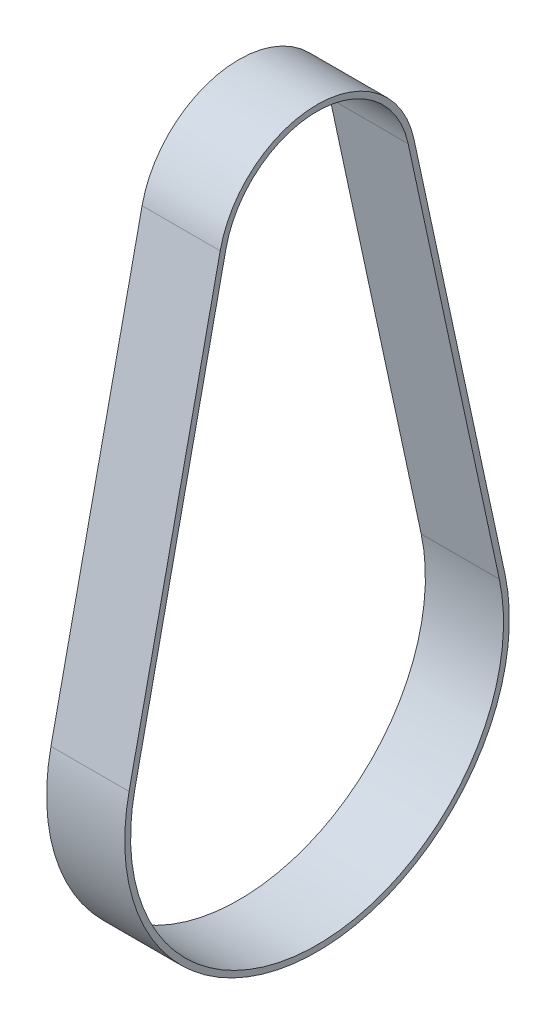
SolidWorks part; units mm, degrees
material "POLYURETHANE (11671)"
ref_plane "Front Plane" through (0, 0, 0) normal (0, 0, 1) x (1, 0, 0)
ref_plane "Top Plane" through (0, 0, 0) normal (0, 1, 0) x (1, 0, 0)
ref_plane "Right Plane" through (0, 0, 0) normal (1, 0, 0) x (0, 0, -1)
sketch "Sketch1" plane through (0, 0, 0) normal (1, 0, 0) x (0, 0, -1)
  line L0 (-37.3369, 8.0507) -> (-18.6694, 94.6255)
  line L1 (37.3369, 8.0507) -> (18.6694, 94.6255)
  line L2 (19.8425, 94.8785) -> (38.5099, 8.3036)
  line L3 (-19.8425, 94.8785) -> (-38.5099, 8.3036)
  arc A0 (-37.3369, 8.0507) -> (37.3369, 8.0507) centre (0, 0) ccw
  arc A1 (18.6694, 94.6255) -> (-18.6694, 94.6255) centre (0, 90.6) ccw
  arc A2 (19.8425, 94.8785) -> (-19.8425, 94.8785) centre (0, 90.6) ccw
  arc A3 (-38.5099, 8.3036) -> (38.5099, 8.3036) centre (0, 0) ccw
  dimension "D1" = 76.39
  dimension "D2" = 38.197
  dimension "D4" = 1.2
  dimension "D3" = 90.6
extrude "Boss-Extrude1" add sketch "Sketch1" along normal blind 16
